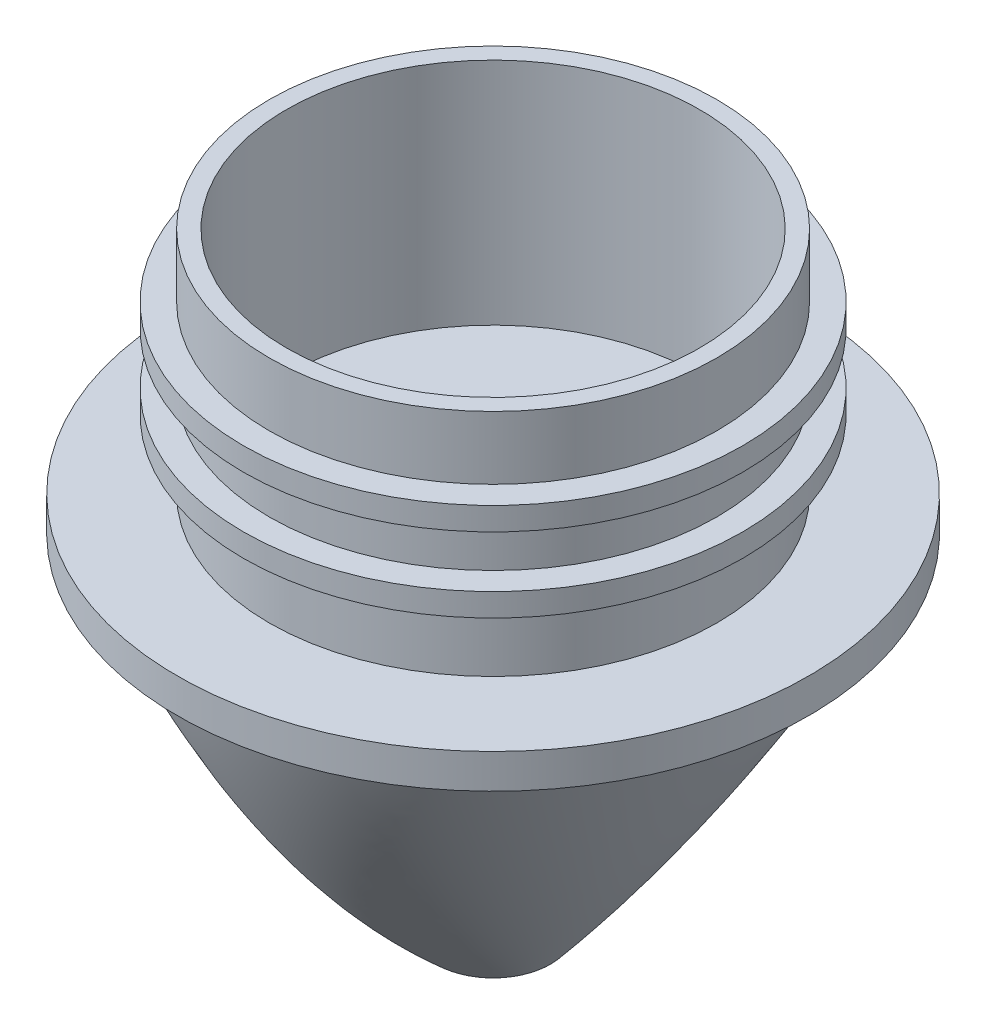
SolidWorks part; units mm, degrees
ref_plane "前基準面" through (0, 0, 0) normal (0, 0, 1) x (1, 0, 0)
ref_plane "上基準面" through (0, 0, 0) normal (0, 1, 0) x (1, 0, 0)
ref_plane "右基準面" through (0, 0, 0) normal (1, 0, 0) x (0, 0, -1)
sketch "草圖1" plane through (0, 0, 0) normal (0, 1, 0) x (1, 0, 0)
  circle A0 centre (0, 0) radius 19.5
  circle A1 centre (0, 0) radius 18
  dimension "D1" = 39
  dimension "D2" = 36
extrude "填料-伸長1" add sketch "草圖1" along normal blind 20
sketch "草圖3" plane through (0, 0, 0) normal (0, -1, 0) x (1, 0, 0)
  circle A0 centre (0, 0) radius 27.5
  dimension "D1" = 55
extrude "填料-伸長2" add sketch "草圖3" along normal blind 3
ref_plane "平面1" through (0, 8, 0) normal (0, 1, 0) x (1, 0, 0)
sketch "草圖4" plane through (0, 8, 0) normal (0, 1, 0) x (1, 0, 0)
  circle A0 centre (0, 0) radius 21.75
  dimension "D1" = 43.5
extrude "填料-伸長3" add sketch "草圖4" against normal blind 2
sketch "草圖6" plane through (0, 0, 0) normal (0, 1, 0) x (1, 0, 0)
  circle A0 centre (0, 0) radius 18
  dimension "D1" = 36
ref_plane "平面2" through (0, 11.5, 0) normal (0, 1, 0) x (1, 0, 0)
sketch "草圖8" plane through (0, 11.5, 0) normal (0, 1, 0) x (1, 0, 0)
  circle A0 centre (0, 0) radius 21.75
extrude "填料-伸長4" add sketch "草圖8" along normal blind 2 from offset 1
extrude "除料-伸長1" cut sketch "草圖6" along normal blind 35
ref_plane "平面3" through (0, -3, 0) normal (0, -1, 0) x (-1, 0, 0)
sketch "草圖10" plane through (0, -3, 0) normal (0, -1, 0) x (-1, 0, 0)
  circle A0 centre (0, 0) radius 25
  dimension "D1" = 50
ref_plane "平面4" through (0, -33, 0) normal (0, -1, 0) x (-1, 0, 0)
sketch "草圖11" plane through (0, -33, 0) normal (0, -1, 0) x (-1, 0, 0)
  circle A0 centre (0, 0) radius 5
  dimension "D1" = 10
sketch "草圖13" plane through (0, 0, 0) normal (1, 0, 0) x (0, 0, -1)
  line L0 (0, -3) -> (0, -45.3687) construction
  line L2 (-25, -3) -> (25, -3) construction
  line L4 (-5, -33) -> (5, -33) construction
  arc A0 (-25, -3) -> (-5, -33) centre (41.6009, 19.734) ccw
  arc A1 (25, -3) -> (5, -33) centre (-41.6009, 19.734) cw
surface "曲面-疊層拉伸2"
surface "曲面-平面1"
surface "曲面-平面2"
surface "曲面-縫織2"
sketch "草圖15" plane through (0, 0, 0) normal (1, 0, 0) x (0, 0, -1)
  line L0 (0, -27.3212) -> (0, -44.2356) construction
  line L1 (-5, -33) -> (0, -33)
  line L2 (-5, -33) -> (5, -33) construction
  line L3 (0, -33) -> (0, -34.9753)
  arc A0 (-5, -33) -> (0, -34.9753) centre (1.6815, -23.4034) ccw
revolve "旋轉10" add sketch "草圖15" angle 360 about L0
sketch "草圖16" plane through (0, 0, 0) normal (1, 0, 0) x (0, 0, -1)
  line L6 (0, 20) -> (0, -45.718) construction
  line L7 (18, 20) -> (-18, 20) construction
  line L12 (-4.9585, -34.1658) -> (-13.1333, -28.1434)
  line L13 (-13.1333, -28.1434) -> (-20.094, -19.8043)
  line L14 (-20.094, -19.8043) -> (-25.0562, -8.7774)
  line L15 (-25.0562, -8.7774) -> (-26.3656, -3)
  line L16 (-30.25, -3) -> (30.25, -3) construction
  line L18 (4.9585, -34.1658) -> (13.1333, -28.1434)
  line L19 (13.1333, -28.1434) -> (20.094, -19.8043)
  line L20 (20.094, -19.8043) -> (25.0562, -8.7774)
  line L21 (25.0562, -8.7774) -> (26.3656, -3)
  line L22 (-26.3656, -3) -> (26.3656, -3)
  line L23 (4.9585, -34.1658) -> (0, -37.132)
  line L24 (-4.9585, -34.1658) -> (0, -37.132)
